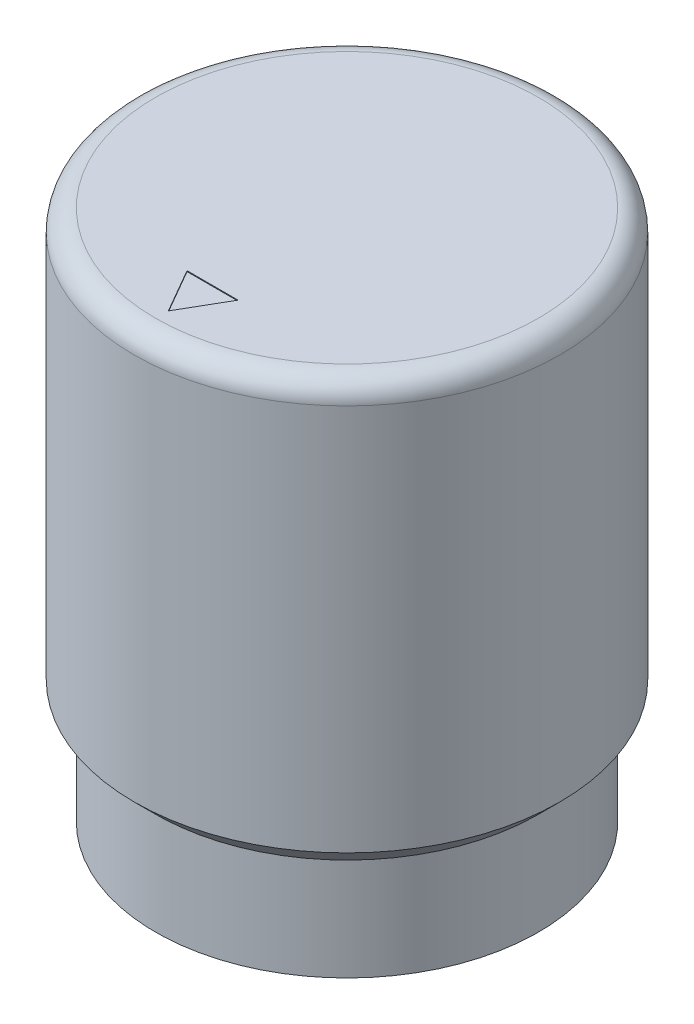
SolidWorks part; units mm, degrees
material "AISI 321 Annealed Stainless Steel (SS)"
ref_plane "Front Plane" through (0, 0, 0) normal (0, 0, 1) x (1, 0, 0)
ref_plane "Top Plane" through (0, 0, 0) normal (0, 1, 0) x (1, 0, 0)
ref_plane "Right Plane" through (0, 0, 0) normal (1, 0, 0) x (0, 0, -1)
sketch "Sketch1" plane through (0, 0, 0) normal (0, 0, 1) x (1, 0, 0)
  line L0 (0, 0) -> (0, 15.875) construction
  line L1 (0, 15.875) -> (6.35, 15.875)
  line L2 (6.35, 15.875) -> (6.35, 3.683)
  line L3 (6.35, 3.683) -> (5.715, 3.048)
  line L4 (5.715, 3.048) -> (5.715, 0)
  line L5 (5.715, 0) -> (4.7625, 0)
  line L6 (4.7625, 0) -> (4.7625, 3.9878)
  line L7 (4.7625, 3.9878) -> (0, 3.9878)
  line L8 (0, 15.875) -> (0, 3.9878)
  point P9 (5.7262, 0)
  point P11 (5.715, 3.0509)
  dimension "D1" = 12.7
  dimension "D2" = 15.875
  dimension "D3" = 9.525
  dimension "D4" = 135
  dimension "D5" = 11.43
  dimension "D6" = 3.9878
  dimension "D7" = 3.048
revolve "Revolve1" add sketch "Sketch1" angle 360 about L0
hole_wizard "1/8 (0.125) Diameter Hole1" positions "Sketch2" profile "Sketch3" hole size "1/8" standard "ANSI Inch"
sketch "Sketch2" plane through (0, 0, 0) normal (0, -1, 0) x (-1, 0, 0)
  point P0 (0, 0)
sketch "Sketch3" plane through (0, 0, 0) normal (1, 0, 0) x (0, 0, -1)
  line L0 (0, 0) -> (0, 13.9079)
  line L1 (0, 13.9079) -> (1.5875, 12.954)
  line L2 (1.5875, 12.954) -> (1.5875, 0)
  line L5 (1.5875, 0) -> (0, 0)
  line L10 (0, 13.9079) -> (-1.5875, 12.954) construction
  line L11 (0, -6.35) -> (0, 107.95) construction
  dimension "Hole Dia." = 3.175
  dimension "Hole Depth" = 12.954
  dimension "Drill Angle" = 118
ref_plane "Plane1" through (0, 0, -6.35) normal (0, 0, -1) x (-1, 0, 0)
hole_wizard "#6-32 Tapped Hole1" positions "Sketch4" profile "Sketch5" tap size "#6-32" standard "ANSI Inch"
sketch "Sketch4" plane through (0, 0, -6.35) normal (0, 0, -1) x (-1, 0, 0)
  point P1 (0, 7.239)
  point P4 (0, 0)
  dimension "D1" = 7.239
sketch "Sketch5" plane through (0, 7.239, -6.35) normal (1, 0, 0) x (0, 1, 0)
  line L0 (0, 0) -> (0, 7.1617)
  line L1 (0, 7.1617) -> (1.3525, 6.349)
  line L2 (1.3525, 6.349) -> (1.3525, 0)
  line L5 (1.3525, 0) -> (0, 0)
  line L10 (0, 7.1617) -> (-1.3526, 6.349) construction
  line L11 (0, -6.35) -> (0, 107.95) construction
  dimension "Tap Drill Dia." = 2.7051
  dimension "Tap Drill Depth" = 6.349
  dimension "Drill Angle" = 118
fillet "Fillet1" radius 0.635 1 edges at (0, 15.875, -6.35)
sketch "Sketch6" plane through (0, 15.875, 0) normal (0, 1, 0) x (1, 0, 0)
  line L0 (0, -5.334) -> (-0.762, -4.0142)
  line L1 (-0.762, -4.0142) -> (0.762, -4.0142)
  line L2 (0.762, -4.0142) -> (0, -5.334)
  circle A1 centre (0, 0) radius 5.715 construction
  point P2 (0, -4.0142)
  dimension "D1" = 1.524
  dimension "D2" = 0.381
extrude "Cut-Extrude1" cut sketch "Sketch6" against normal blind 0.0254
